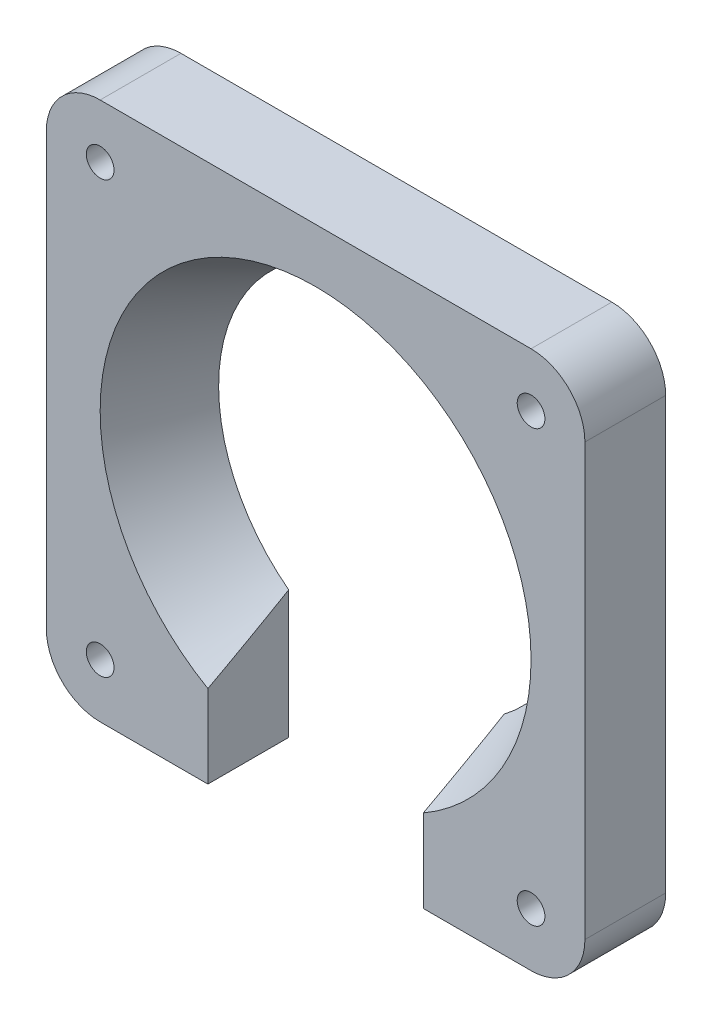
SolidWorks part; units mm, degrees
ref_plane "Front Plane" through (0, 0, 0) normal (0, 0, 1) x (1, 0, 0)
ref_plane "Top Plane" through (0, 0, 0) normal (0, 1, 0) x (1, 0, 0)
ref_plane "Right Plane" through (0, 0, 0) normal (1, 0, 0) x (0, 0, -1)
sketch "Sketch1" plane through (0, 0, 0) normal (0, 0, 1) x (1, 0, 0)
  line L1 (-27.3499, 25.4518) -> (36.1501, 25.4518)
  line L2 (-27.3499, 25.4518) -> (-27.3499, -38.0482)
  line L3 (-27.3499, -38.0482) -> (36.1501, -38.0482)
  line L4 (36.1501, 25.4518) -> (36.1501, -38.0482)
  dimension "D1" = 63.5
  dimension "D2" = 63.5
extrude "Boss-Extrude1" add sketch "Sketch1" along normal blind 9.525
sketch "Sketch2" plane through (0, 0, 9.525) normal (0, 0, 1) x (1, 0, 0)
  line L0 (4.4001, 25.4518) -> (4.4001, -38.0482) construction
  line L1 (36.1501, 25.4518) -> (-27.3499, 25.4518) construction
  line L2 (-27.3499, -38.0482) -> (36.1501, -38.0482) construction
  line L3 (-27.3499, -6.2982) -> (36.1501, -6.2982) construction
  line L4 (-27.3499, 25.4518) -> (-27.3499, -38.0482) construction
  line L5 (36.1501, -38.0482) -> (36.1501, 25.4518) construction
  circle A0 centre (4.4001, -6.2982) radius 25.4
  dimension "D1" = 50.8
extrude "Cut-Extrude1" cut sketch "Sketch2" against normal blind 12.7 draft 25
sketch "Sketch3" plane through (0, 0, 9.525) normal (0, 0, 1) x (1, 0, 0)
  line L0 (4.4001, -38.0482) -> (4.4001, 25.4518) construction
  line L1 (-27.3499, -38.0482) -> (36.1501, -38.0482) construction
  line L2 (36.1501, 25.4518) -> (-27.3499, 25.4518) construction
  line L4 (-8.2999, -38.0482) -> (17.1001, -38.0482)
  line L5 (-8.2999, -38.0482) -> (-8.2999, -9.2616)
  line L6 (-8.2999, -9.2616) -> (17.1001, -9.2616)
  line L7 (17.1001, -38.0482) -> (17.1001, -9.2616)
  dimension "D1" = 25.4
  dimension "D2" = 12.7
extrude "Cut-Extrude2" cut sketch "Sketch3" against normal up to surface (9.525 mm away) up to face at (25.3586, -6.2982, 0)
sketch "Sketch4" plane through (0, 0, 9.525) normal (0, 0, 1) x (1, 0, 0)
  line L0 (36.1501, 25.4518) -> (-27.3499, 25.4518) construction
  line L1 (-27.3499, 25.4518) -> (-27.3499, -38.0482) construction
  circle A0 centre (-20.9999, 19.1018) radius 1.632
  circle A1 centre (29.8001, 19.1018) radius 1.632
  circle A2 centre (29.8001, -31.6982) radius 1.6319
  circle A3 centre (-20.9999, -31.6982) radius 1.632
  dimension "D1" = 3.2639
  dimension "D2" = 6.35
  dimension "D3" = 6.35
  dimension "D4" = 2
  dimension "D5" = 2
extrude "Cut-Extrude3" cut sketch "Sketch4" against normal up to surface (9.525 mm away) up to face at (4.4001, -13.7, 0)
fillet "Fillet1" radius 6.35 3 edges at (-27.3499, 25.4518, 4.7625) (36.1501, 25.4518, 4.7625) (-27.3499, -38.0482, 4.7625)
fillet "Fillet2" radius 6.35 1 edges at (36.1501, -38.0482, 4.7625)
